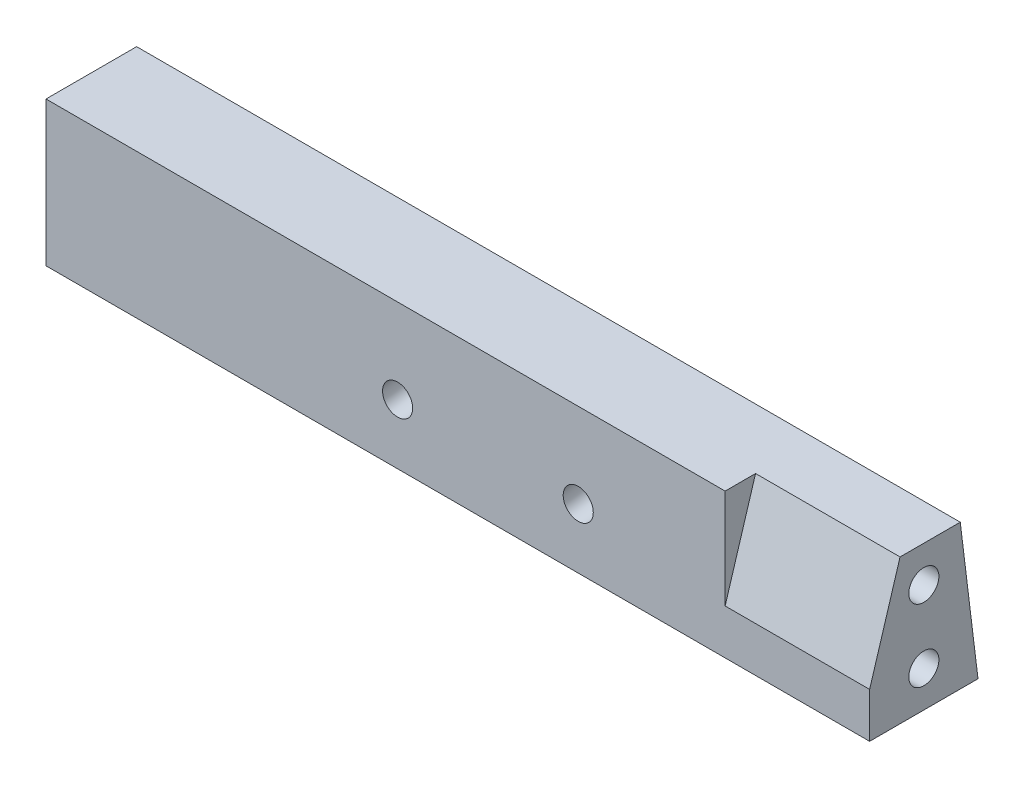
SolidWorks part; units mm, degrees
ref_plane "Plano frontal" through (0, 0, 0) normal (0, 0, 1) x (1, 0, 0)
ref_plane "Plano superior" through (0, 0, 0) normal (0, 1, 0) x (1, 0, 0)
ref_plane "Plano direito" through (0, 0, 0) normal (1, 0, 0) x (0, 0, -1)
sketch "Esboço1" plane through (0, 0, 0) normal (1, 0, 0) x (0, 0, -1)
  line L0 (4.5, -6) -> (3.0266, 6) construction
  line L1 (-4.5, -6) -> (4.5, -6)
  line L2 (-4.5, -6) -> (-4.5, 6)
  line L3 (-4.5, 6) -> (4.5, 6) construction
  line L4 (4.5, -6) -> (4.5, 6) construction
  line L5 (-4.5, -6) -> (4.5, 6) construction
  line L6 (-4.5, 6) -> (4.5, -6) construction
  line L7 (3.0266, 6) -> (4.5, -6)
  line L8 (-4.5, 6) -> (3.0266, 6)
  line L9 (3.7633, 0) -> (-4.5, -1.0146) construction
  point P0 (0, 0)
  dimension "D1" = 12
  dimension "D2" = 9
  dimension "D3" = 7
extrude "Ressalto-extrusão1" add sketch "Esboço1" along normal blind 68.4
sketch "Esboço2" plane through (68.4, 0, 0) normal (1, 0, 0) x (0, 0, -1)
  line L0 (-4.5, -2.2641) -> (-1.9734, 6) construction
  line L1 (-4.5, 6) -> (-4.5, -6) construction
  line L2 (-1.9734, 6) -> (-4.5, -2.2641)
  line L3 (-4.5, -2.2641) -> (-4.5, 6)
  line L4 (-4.5, 6) -> (-4.5, -6)
  line L5 (-4.5, -6) -> (4.5, -6)
  line L6 (4.5, -6) -> (3.0266, 6)
  line L7 (3.0266, 6) -> (-4.5, 6)
  line L8 (-4.5, 6) -> (-4.5, -6) construction
  line L9 (-4.5, -6) -> (4.5, -6) construction
  line L10 (4.5, -6) -> (3.0266, 6) construction
  line L11 (3.0266, 6) -> (-4.5, 6) construction
  line L12 (-4.5, 6) -> (-1.9734, 6)
  dimension "D2" = 17
  dimension "D3" = 5
  dimension "D1" = 0
extrude "Corte-extrusão1" cut sketch "Esboço2" against normal blind 12
sketch "Esboço3" plane through (68.4, 0, 0) normal (1, 0, 0) x (0, 0, -1)
  line L1 (3.0266, 6) -> (-1.9734, 6) construction
  line L2 (-4.5, -6) -> (4.5, -6) construction
  line L3 (0, -6) -> (0, 6) construction
  point P0 (0, 3)
  point P10 (0, -3)
  dimension "D1" = 3
  dimension "D2" = 3
hole_wizard "Furo roscado de M3x0.51" positions "Esboço5" profile "Esboço4" tap size "M3x0.5" standard "Ansi Metric"
sketch "Esboço5" plane through (68.4, 0, 0) normal (1, 0, 0) x (0, 0, -1)
  point P0 (0, -3)
  point P3 (0, 3)
cosmetic thread "Rosca de furo1"
cosmetic thread "Rosca de furo2"
sketch "Esboço4" plane through (68.4, -3, 0) normal (0, 1, 0) x (0, 0, -1)
  line L0 (0, 0) -> (0, 9.2511)
  line L1 (0, 9.2511) -> (1.25, 8.5)
  line L2 (1.25, 8.5) -> (1.25, 0)
  line L5 (1.25, 0) -> (0, 0)
  line L10 (0, 9.2511) -> (-1.25, 8.5) construction
  line L11 (0, -6.35) -> (0, 107.95) construction
  dimension "Tap Drill Dia." = 2.5
  dimension "Tap Drill Depth" = 8.5
  dimension "Drill Angle" = 118
sketch "Esboço6" plane through (0, 0, 0) normal (-1, 0, 0) x (0, 0, 1)
  line L0 (0, -6) -> (0, 6) construction
  line L1 (4.5, -6) -> (-4.5, -6) construction
  line L2 (-3.0266, 6) -> (4.5, 6) construction
  point P7 (0, -3)
  point P8 (0, 3)
  dimension "D1" = 3
  dimension "D2" = 3
hole_wizard "Furo roscado de M3x0.52" positions "Esboço8" profile "Esboço7" tap size "M3x0.5" standard "Ansi Metric"
sketch "Esboço8" plane through (0, 0, 0) normal (-1, 0, 0) x (0, 0, 1)
  point P0 (0, 3)
  point P3 (0, -3)
sketch "Esboço7" plane through (0, 3, 0) normal (0, 1, 0) x (0, 0, 1)
  line L0 (0, 0) -> (0, 9.2511)
  line L1 (0, 9.2511) -> (1.25, 8.5)
  line L2 (1.25, 8.5) -> (1.25, 0)
  line L5 (1.25, 0) -> (0, 0)
  line L10 (0, 9.2511) -> (-1.25, 8.5) construction
  line L11 (0, -6.35) -> (0, 107.95) construction
  dimension "Tap Drill Dia." = 2.5
  dimension "Tap Drill Depth" = 8.5
  dimension "Drill Angle" = 118
cosmetic thread "Rosca de furo3"
cosmetic thread "Rosca de furo4"
sketch "Esboço9" plane through (0, 0.4552, -3.7074) normal (0, 0.1219, -0.9925) x (-1, 0, 0)
  circle A1 centre (-29.2, -0.4644) radius 1.5
  circle A2 centre (-29.2, -0.4644) radius 1.5 construction
  circle A3 centre (-44.2, -0.4644) radius 1.5
  circle A4 centre (-44.2, -0.4644) radius 1.5 construction
  dimension "D1" = 0
  dimension "D2" = 0
hole_wizard "Furo roscado de M3x0.53" positions "Esboço11" profile "Esboço12" tap size "M3x0.5" standard "Ansi Metric"
sketch "Esboço11" plane through (0, 0.4552, -3.7074) normal (0, 0.1219, -0.9925) x (-1, 0, 0)
  point P0 (-29.2, -0.4644)
  point P3 (-44.2, -0.4644)
sketch "Esboço12" plane through (29.2, -0.0058, -3.764) normal (1, 0, 0) x (0, 0.9925, 0.1219)
  line L0 (0, 0) -> (0, 8.3261)
  line L1 (0, 8.3261) -> (1.25, 8.3261)
  line L2 (1.25, 8.3261) -> (1.25, 0)
  line L5 (1.25, 0) -> (0, 0)
  line L11 (0, -6.35) -> (0, 107.95) construction
  dimension "Thru Tap Drill Dia." = 2.5
  dimension "Thru Tap Drill Depth" = 8.3261
cosmetic thread "Rosca de furo5"
cosmetic thread "Rosca de furo6"
